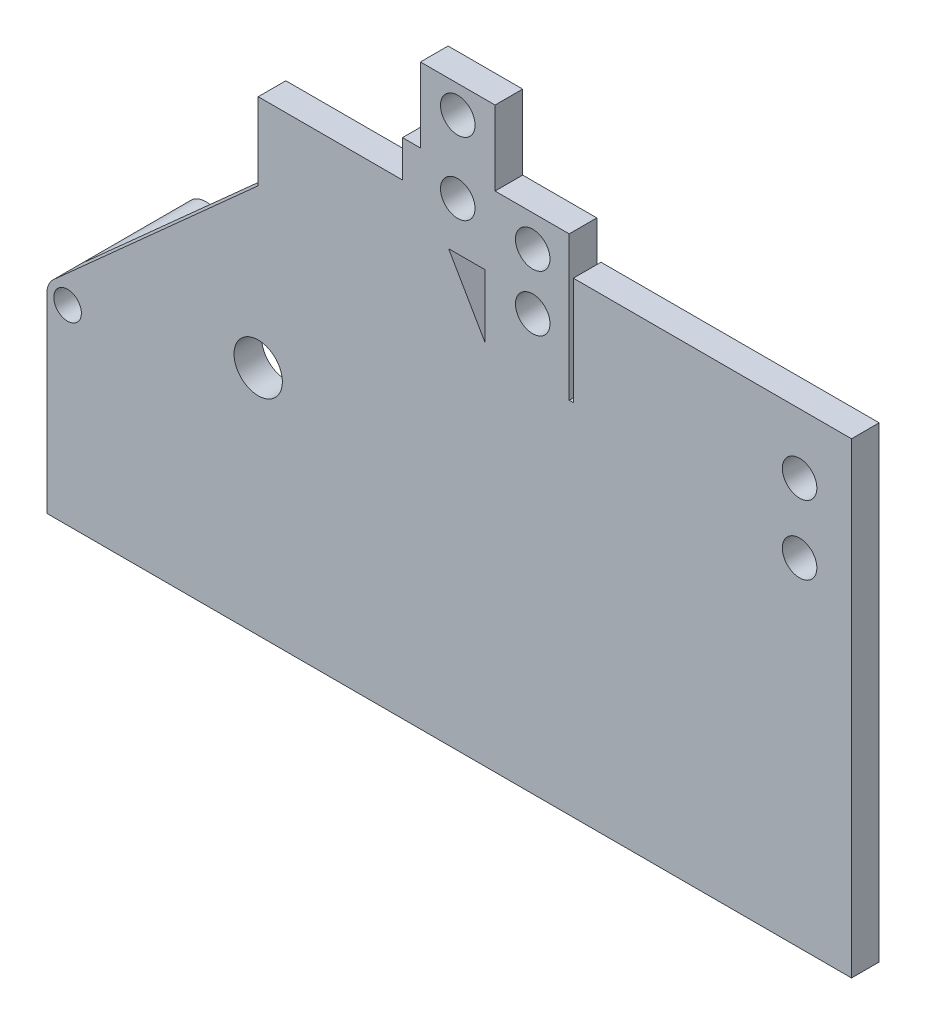
SolidWorks part; units mm, degrees
ref_plane "Front Plane" through (0, 0, 0) normal (0, 0, 1) x (1, 0, 0)
ref_plane "Top Plane" through (0, 0, 0) normal (0, 1, 0) x (1, 0, 0)
ref_plane "Right Plane" through (0, 0, 0) normal (1, 0, 0) x (0, 0, -1)
sketch "Sketch1" plane through (0, 0, 0) normal (0, 0, 1) x (1, 0, 0)
  line L0 (-54.9958, 0) -> (67.63, 0) construction
  line L1 (0, 23.262) -> (0, -27.492) construction
  line L2 (0, 0) -> (582.5, 0)
  line L3 (0, 0) -> (0, 138)
  line L4 (522.5, 60) -> (572.5, 51.1837)
  line L5 (582.5, 0) -> (582.5, 51.1837)
  line L6 (582.5, 51.1837) -> (572.5, 51.1837)
  line L8 (4.9848, 149.1667) -> (129.7305, 261.0488)
  line L10 (129.7305, 261.0488) -> (153, 281.9188)
  line L11 (153, 281.9188) -> (153, 337.7402)
  line L13 (244.94, 310.7333) -> (374.6494, 86.07)
  line L15 (522.5, 60) -> (374.6494, 86.07)
  circle A0 centre (15, 138) radius 15
  circle A2 centre (15, 138) radius 10
  arc A4 (244.94, 310.7333) -> (153, 337.7402) centre (153, 167.7402) ccw
  circle A5 centre (153, 167.7402) radius 17.5
  point P15 (153, 167.7402)
  dimension "D3" = 30
  dimension "D2" = 170
  dimension "D1" = 582.5
extrude "Boss-Extrude1" add sketch "Sketch1" along normal blind 20
sketch "Sketch2" plane through (0, 0, 20) normal (0, 0, 1) x (1, 0, 0)
  circle A0 centre (15, 138) radius 10
  circle A1 centre (15, 138) radius 15
extrude "Boss-Extrude2" add sketch "Sketch2" against normal blind 100
sketch "Sketch3" plane through (0, 0, 0) normal (0, 0, -1) x (-1, 0, 0)
  circle A0 centre (-15, 138) radius 24.4466
  circle A1 centre (-153, 167.7402) radius 60.5372
sketch "Sketch4" plane through (0, 0, 20) normal (0, 0, 1) x (1, 0, 0)
  line L0 (153, 167.7402) -> (535.4044, 167.7402) construction
  line L1 (153, 167.7402) -> (153, 389.688) construction
  line L2 (153, 167.7402) -> (281.8848, 326.8997) construction
  line L3 (426.1731, 76.985) -> (522.5, 60)
  line L8 (153, 337.7402) -> (257.4605, 337.7402)
  line L9 (0, 0) -> (582.5, 0) construction
  line L10 (290.8428, 311.384) -> (426.1731, 76.985)
  line L11 (244.94, 310.7333) -> (374.6494, 86.07) construction
  line L12 (374.6494, 86.07) -> (426.1731, 76.985)
  line L13 (374.6494, 86.07) -> (244.94, 310.7333)
  line L18 (290.8428, 311.384) -> (257.4605, 311.384)
  line L19 (257.4605, 337.7402) -> (257.4605, 311.384)
  arc A4 (244.94, 310.7333) -> (153, 337.7402) centre (153, 167.7402) ccw
  line M13 (572.5, 51.1837) -> (374.6494, 86.07)
  line M14 (374.6494, 86.07) -> (244.94, 310.7333)
  arc M15 (244.94, 310.7333) -> (153, 337.7402) centre (153, 167.7402) ccw
  dimension "D1" = 51
extrude "Boss-Extrude6" add sketch "Sketch4" against normal blind 20 contours L19 L8 L10 L18 M15 M14 M13
sketch "Sketch9" plane through (0, 0, 20) normal (0, 0, 1) x (1, 0, 0)
  line L1 (320.5094, 260) -> (522.5, 260)
  line L2 (290.8428, 311.384) -> (426.1731, 76.985) construction
  line L3 (0, 0) -> (582.5, 0) construction
  line L4 (320.5094, 260) -> (426.1731, 76.985)
  line L5 (426.1731, 76.985) -> (522.5, 60)
  line L6 (522.5, 260) -> (582.5, 260)
  line L8 (522.5, 60) -> (572.5, 51.1837)
  line L9 (582.5, 260) -> (582.5, 51.1837)
  line L10 (582.5, 51.1837) -> (572.5, 51.1837)
extrude "Boss-Extrude7" add sketch "Sketch9" against normal blind 20
sketch "Sketch10" plane through (0, 0, 20) normal (0, 0, 1) x (1, 0, 0)
  line L0 (257.4605, 364.3202) -> (257.4605, 337.7402)
  line L1 (257.4605, 364.3202) -> (317.1805, 364.3202)
  line L2 (317.1805, 364.3202) -> (317.1805, 311.384)
  line L3 (257.4605, 311.384) -> (317.1805, 311.384)
  line L4 (257.4605, 337.7402) -> (257.4605, 311.384)
  line L5 (324.4605, 418.2516) -> (324.4605, 364.3202)
  line L7 (582.5, 260) -> (320.5094, 260) construction
  line L9 (347.6505, 321.2239) -> (317.1805, 321.2239)
  line L10 (347.6505, 321.2239) -> (378.1205, 321.2239)
  line L11 (378.1205, 321.2239) -> (378.1205, 364.3202)
  line L12 (378.1205, 364.3202) -> (317.1805, 364.3202)
  line L13 (270.4605, 364.3202) -> (270.4605, 418.2516)
  line L14 (270.4605, 418.2516) -> (324.4605, 418.2516)
  line L16 (378.1205, 321.2239) -> (378.1205, 260)
  line L17 (378.1205, 260) -> (320.5094, 260)
  line L18 (317.1805, 265.7096) -> (317.1805, 311.384)
  line L19 (320.5094, 260) -> (317.1805, 265.7096)
  line L21 (290.8428, 311.384) -> (257.4605, 311.384) construction
  circle A0 centre (297.4605, 346.134) radius 12.5
  circle A1 centre (351.7105, 341.56) radius 12.5
  circle A2 centre (351.7105, 301) radius 12.5
  circle A3 centre (297.4605, 398.384) radius 12.5
  circle A4 centre (544.8957, 294.5162) radius 12.5
  circle A5 centre (544.8957, 244.5162) radius 12.5
  point P29 (544.8957, 244.5162)
  point P36 (544.8957, 294.5162)
  line M5 (582.5, 260) -> (320.5094, 260)
  line M6 (320.5094, 260) -> (290.8428, 311.384)
  line M7 (290.8428, 311.384) -> (257.4605, 311.384)
  line M8 (257.4605, 311.384) -> (257.4605, 337.7402)
  dimension "D2" = 54.25
  dimension "D1" = 40.56
extrude "Boss-Extrude9" add sketch "Sketch10" against normal blind 20 separate body contours L14 L13 L1 L12 L5 A3 | L3 L2 L1 L0 A0 M7 M8 | L11 L12 L2 L9 L10 A1 | L18 L16 L10 L9 L2 A2 M6 M5
sketch "Sketch14" plane through (0, 0, 0) normal (0, 0, -1) x (-1, 0, 0)
  line L0 (-320.5094, 260) -> (-426.1731, 76.985)
  line L1 (-426.1731, 76.985) -> (-522.5, 60)
  line L5 (-522.5, 338.0456) -> (-582.5, 338.0456)
  line L6 (-381.1194, 260) -> (-381.1194, 338.0456)
  line L7 (-381.1194, 338.0456) -> (-522.5, 338.0456)
  line L9 (-381.1194, 260) -> (-320.5094, 260)
  line L12 (-582.5, 338.0456) -> (-582.5, 60)
  line L13 (-522.5, 60) -> (-572.5, 60)
  line L14 (-582.5, 60) -> (-572.5, 60)
  dimension "D1" = 60.61
extrude "Boss-Extrude10" add sketch "Sketch14" against normal blind 20
sketch "Sketch16" plane through (0, 0, 20) normal (0, 0, 1) x (1, 0, 0)
  line L0 (351.7105, 301) -> (351.7105, 341.56) construction
  line L1 (351.7105, 321.28) -> (373.2641, 321.28)
  line L2 (351.7105, 321.28) -> (544.8957, 269.5162) construction
  line L3 (544.8957, 269.5162) -> (544.8957, 294.5162) construction
  line L4 (544.8957, 269.5162) -> (544.8957, 244.5162) construction
  circle A0 centre (544.8957, 294.5162) radius 12.5
  circle A1 centre (544.8957, 244.5162) radius 12.5
  circle A2 centre (544.8957, 294.5162) radius 20.1908
  dimension "D1" = 15
  dimension "D2" = 200
  dimension "D3" = 25
  dimension "D4" = 25
extrude "Cut-Extrude1" cut sketch "Sketch16" against normal blind 20 contours A0 | A1
